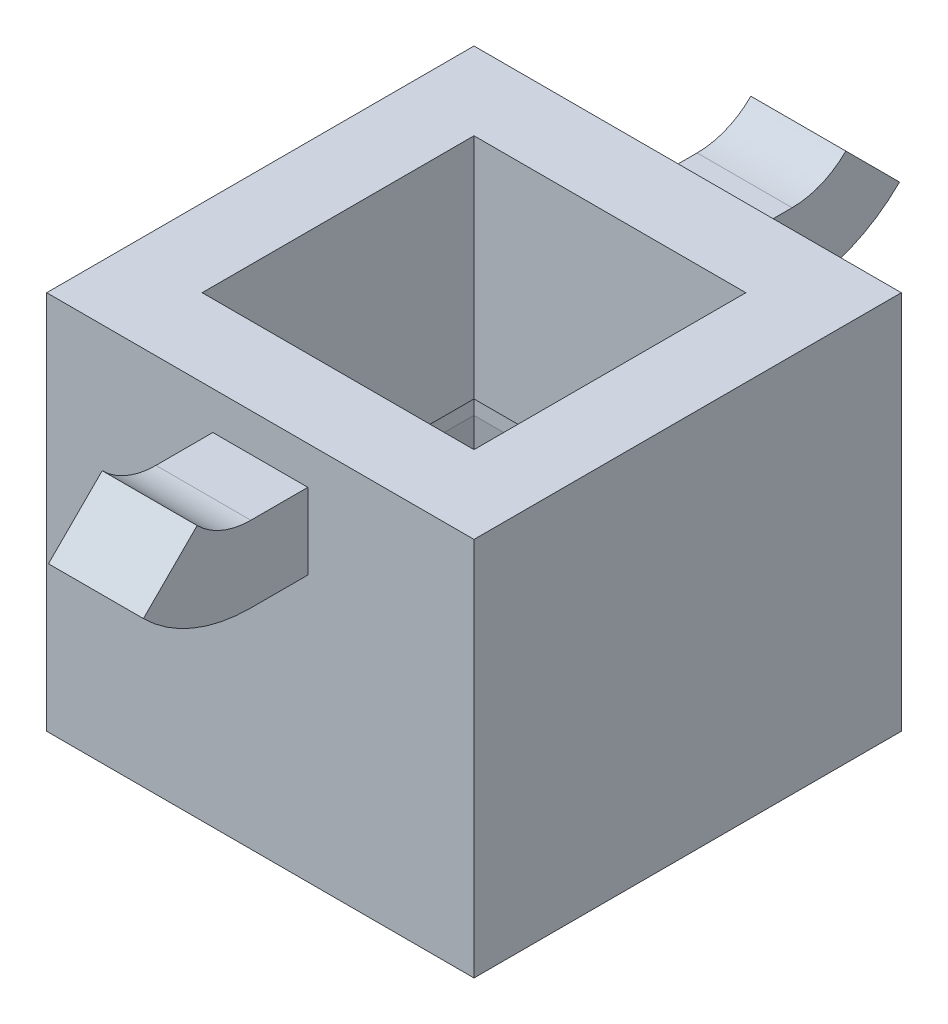
SolidWorks part; units mm, degrees
ref_plane "Front Plane" through (0, 0, 0) normal (0, 0, 1) x (1, 0, 0)
ref_plane "Top Plane" through (0, 0, 0) normal (0, 1, 0) x (1, 0, 0)
ref_plane "Right Plane" through (0, 0, 0) normal (1, 0, 0) x (0, 0, -1)
sketch "Sketch1" plane through (0, 0, 0) normal (0, 1, 0) x (1, 0, 0)
  line L1 (11.25, -11.25) -> (-11.25, -11.25)
  line L2 (11.25, -11.25) -> (11.25, 11.25)
  line L3 (11.25, 11.25) -> (-11.25, 11.25)
  line L4 (-11.25, -11.25) -> (-11.25, 11.25)
  line L5 (11.25, -11.25) -> (-11.25, 11.25) construction
  line L6 (11.25, 11.25) -> (-11.25, -11.25) construction
  point P0 (0, 0)
  dimension "D1" = 22.5
extrude "Boss-Extrude1" add sketch "Sketch1" along normal blind 20
sketch "Sketch3" plane through (0, 0, 0) normal (0, -1, 0) x (1, 0, 0)
  line L1 (-9.25, -9.25) -> (9.25, -9.25)
  line L2 (-9.25, -9.25) -> (-9.25, 9.25)
  line L3 (-9.25, 9.25) -> (9.25, 9.25)
  line L4 (9.25, -9.25) -> (9.25, 9.25)
  line L5 (-9.25, -9.25) -> (9.25, 9.25) construction
  line L6 (-9.25, 9.25) -> (9.25, -9.25) construction
  point P0 (0, 0)
  dimension "D1" = 18.5
sketch "Sketch5" plane through (0, 0, -11.25) normal (0, 0, -1) x (-1, 0, 0)
  line L0 (-11.25, 0) -> (11.25, 20) construction
  line L1 (-11.25, 20) -> (11.25, 0) construction
  line L2 (0, 16) -> (0, 10) construction
  line L3 (2.5, 18) -> (-2.5, 18)
  line L4 (2.5, 18) -> (2.5, 14)
  line L5 (2.5, 14) -> (-2.5, 14)
  line L6 (-2.5, 18) -> (-2.5, 14)
  line L7 (2.5, 18) -> (-2.5, 14) construction
  line L8 (2.5, 14) -> (-2.5, 18) construction
  dimension "D1" = 5
  dimension "D2" = 4
  dimension "D3" = 6
sketch "Sketch6" plane through (0, 0, 0) normal (1, 0, 0) x (0, 0, -1)
  line L0 (11.25, 16) -> (14.25, 16)
  arc A0 (14.25, 16) -> (18.4926, 17.7574) centre (14.25, 22) ccw
  dimension "D2" = 6
  dimension "D1" = 3
sweep "Sweep1" add profiles "Sketch5" path "Sketch6"
mirror "Mirror1" about plane through (0, 0, 0) normal (0, 0, 1) of "Sweep1"
extrude "Cut-Extrude5" cut sketch "Sketch3" against normal blind 6 draft 8
sketch "Sketch14" plane through (0, 6, 0) normal (0, -1, 0) x (1, 0, 0)
  line L1 (8.4068, 8.4068) -> (-8.4068, 8.4068)
  line L2 (8.4068, 8.4068) -> (8.4068, -8.4068)
  line L3 (8.4068, -8.4068) -> (-8.4068, -8.4068)
  line L4 (-8.4068, 8.4068) -> (-8.4068, -8.4068)
  line L5 (8.4068, 8.4068) -> (-8.4068, -8.4068) construction
  line L6 (8.4068, -8.4068) -> (-8.4068, 8.4068) construction
  point P0 (0, 0)
extrude "Cut-Extrude6" cut sketch "Sketch14" against normal blind 2
sketch "Sketch15" plane through (0, 8, 0) normal (0, -1, 0) x (1, 0, 0)
  line L0 (8.4068, 8.4068) -> (-8.4068, 8.4068) construction
  line L1 (7.1568, -7.1568) -> (-7.1568, -7.1568)
  line L2 (7.1568, -7.1568) -> (7.1568, 7.1568)
  line L3 (7.1568, 7.1568) -> (-7.1568, 7.1568)
  line L4 (-7.1568, -7.1568) -> (-7.1568, 7.1568)
  line L5 (7.1568, -7.1568) -> (-7.1568, 7.1568) construction
  line L6 (7.1568, 7.1568) -> (-7.1568, -7.1568) construction
  point P0 (0, 0)
  dimension "D1" = 1.25
extrude "Cut-Extrude7" cut sketch "Sketch15" against normal up to next
